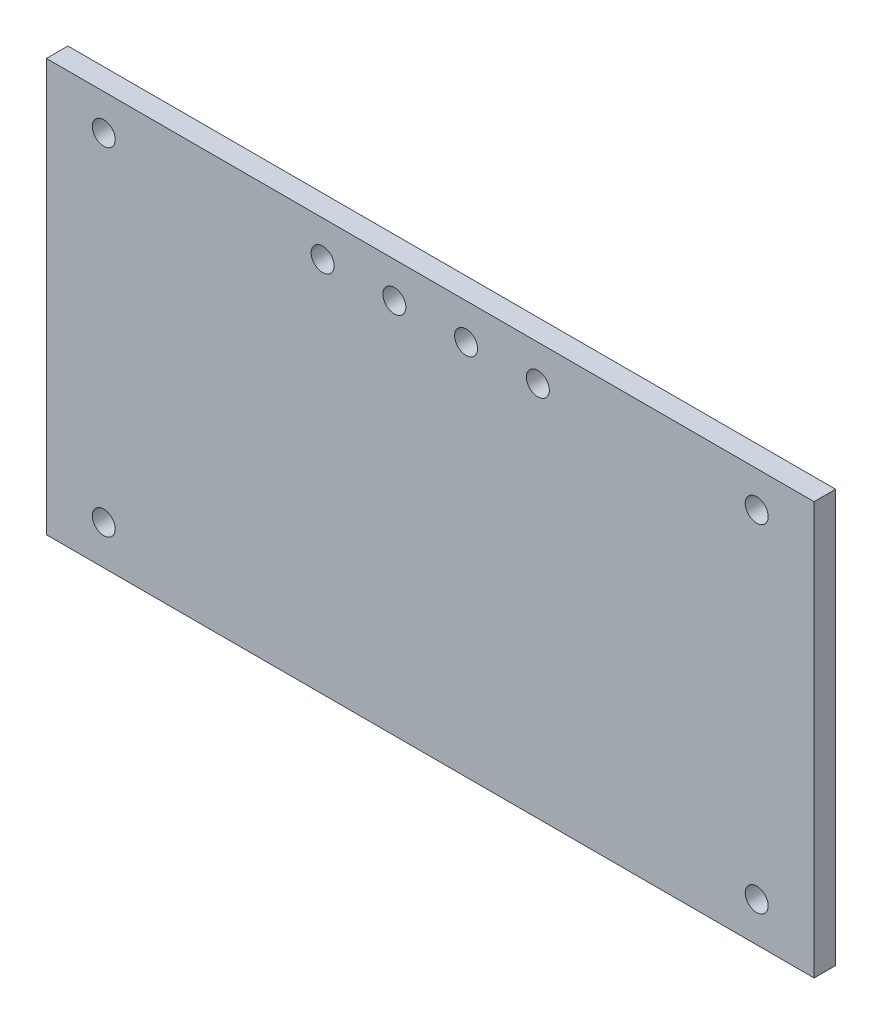
SolidWorks part; units mm, degrees
material "Thornel Mat VMA"
ref_plane "前视基准面" through (0, 0, 0) normal (0, 0, 1) x (1, 0, 0)
ref_plane "上视基准面" through (0, 0, 0) normal (0, 1, 0) x (1, 0, 0)
ref_plane "右视基准面" through (0, 0, 0) normal (1, 0, 0) x (0, 0, -1)
other "Configuration Table"
sketch "草图1" plane through (0, 0, 0) normal (0, 0, 1) x (1, 0, 0)
  line L0 (29.576, 31.8307) -> (29.576, 26.8307) construction
  line L1 (-15.924, 26.8307) -> (75.076, 26.8307) construction
  line L2 (-15.924, 26.8307) -> (-15.924, -20.1693) construction
  line L3 (-15.924, -20.1693) -> (75.076, -20.1693) construction
  line L4 (75.076, 26.8307) -> (75.076, -20.1693) construction
  line L5 (-23.924, 31.8307) -> (83.076, 31.8307)
  line L6 (-23.924, 31.8307) -> (-23.924, -25.6649)
  line L7 (-23.924, -25.6649) -> (83.076, -25.6649)
  line L8 (83.076, 31.8307) -> (83.076, -25.6649)
  circle A0 centre (-15.924, 26.8307) radius 1.6
  circle A1 centre (-15.924, -20.1693) radius 1.6
  circle A2 centre (75.076, -20.1693) radius 1.6
  circle A3 centre (75.076, 26.8307) radius 1.6
  circle A4 centre (14.576, 26.8307) radius 1.6
  circle A5 centre (24.576, 26.8307) radius 1.6
  circle A6 centre (34.576, 26.8307) radius 1.6
  circle A7 centre (44.576, 26.8307) radius 1.6
  dimension "D3" = 3.2
  dimension "D5" = 5
  dimension "D9" = 3.2
  dimension "D1" = 91
  dimension "D2" = 47
  dimension "D4" = 8
  dimension "D6" = 10
  dimension "D7" = 5
  dimension "D8" = 10
  dimension "D10" = 5
extrude "凸台-拉伸1" add sketch "草图1" along normal blind 3
